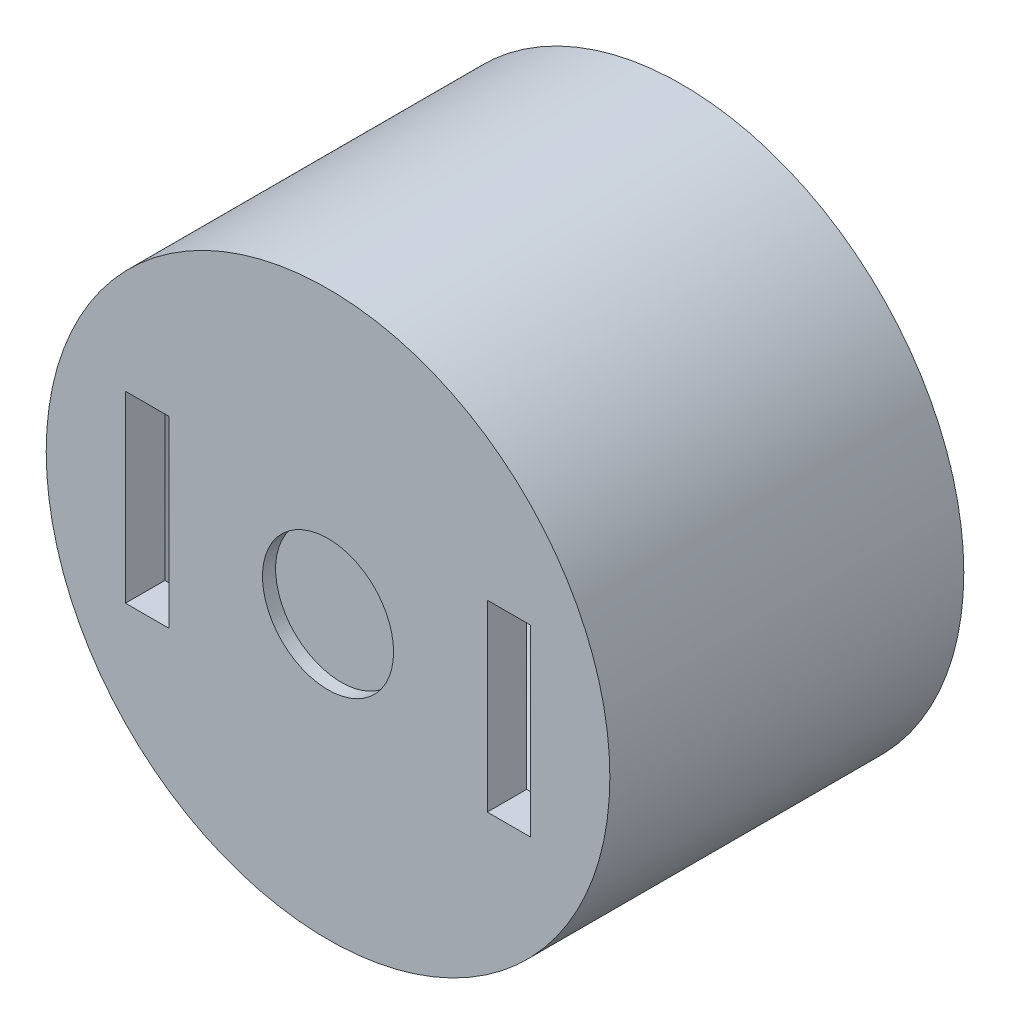
SolidWorks part; units mm, degrees
ref_plane "Front Plane" through (0, 0, 0) normal (0, 0, 1) x (1, 0, 0)
ref_plane "Top Plane" through (0, 0, 0) normal (0, 1, 0) x (1, 0, 0)
ref_plane "Right Plane" through (0, 0, 0) normal (1, 0, 0) x (0, 0, -1)
sketch "Sketch1" plane through (0, 0, 0) normal (0, 0, 1) x (1, 0, 0)
  circle A0 centre (0, 0) radius 21.5
extrude "Boss-Extrude1" add sketch "Sketch1" along normal blind 27
sketch "Sketch2" plane through (0, 0, 0) normal (0, 0, 1) x (1, 0, 0)
  circle A0 centre (0, 0) radius 18.75
extrude "Cut-Extrude2" cut sketch "Sketch2" along normal blind 24
sketch "Sketch4" plane through (0, 0, 0) normal (0, 0, 1) x (1, 0, 0)
  line L1 (15.45, 7) -> (12.15, 7)
  line L4 (15.45, 7) -> (15.45, -7)
  line L5 (15.45, -7) -> (12.15, -7)
  line L6 (12.15, 7) -> (12.15, -7)
  line L7 (15.45, 7) -> (12.15, -7) construction
  line L8 (15.45, -7) -> (12.15, 7) construction
  line L9 (-15.45, 7) -> (-12.15, 7)
  line L10 (-15.45, 7) -> (-15.45, -7)
  line L11 (-15.45, -7) -> (-12.15, -7)
  line L12 (-12.15, 7) -> (-12.15, -7)
  line L13 (-15.45, 7) -> (-12.15, -7) construction
  line L14 (-15.45, -7) -> (-12.15, 7) construction
extrude "Cut-Extrude6" cut sketch "Sketch4" along normal blind 32
sketch "Sketch7" plane through (0, 0, 27) normal (0, 0, 1) x (1, 0, 0)
  circle A0 centre (0, 0) radius 5
extrude "Cut-Extrude8" cut sketch "Sketch7" against normal blind 1
